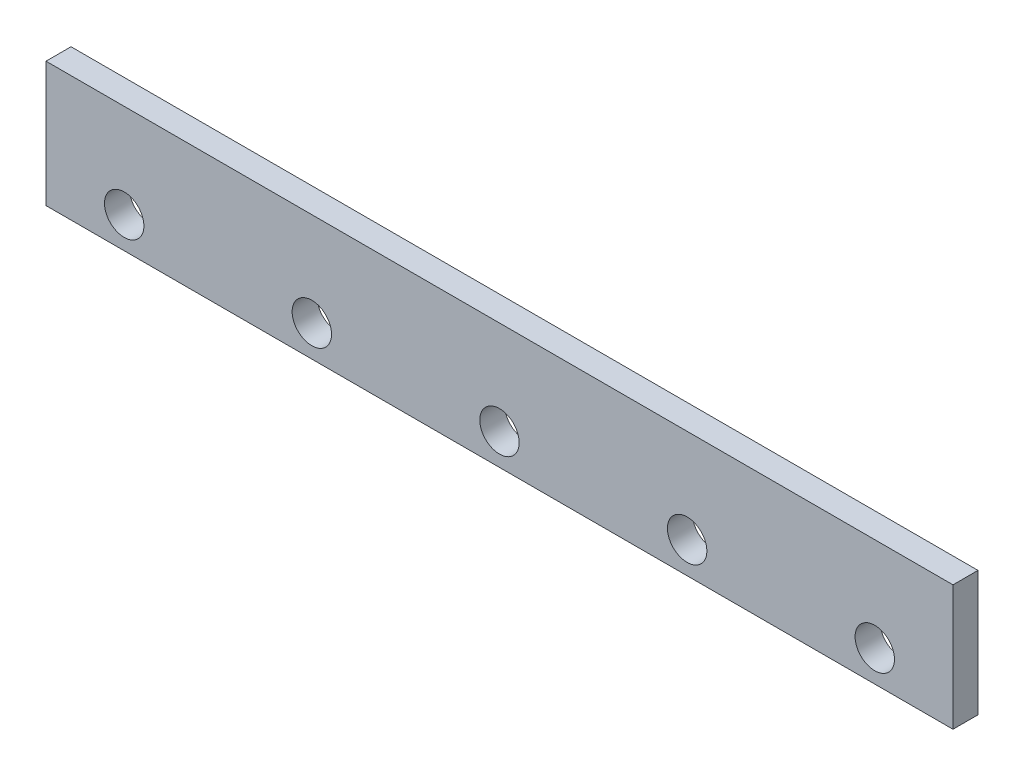
SolidWorks part; units mm, degrees
ref_plane "Front Plane" through (0, 0, 0) normal (0, 0, 1) x (1, 0, 0)
ref_plane "Top Plane" through (0, 0, 0) normal (0, 1, 0) x (1, 0, 0)
ref_plane "Right Plane" through (0, 0, 0) normal (1, 0, 0) x (0, 0, -1)
sketch "Sketch1" plane through (0, 0, 0) normal (0, 0, 1) x (1, 0, 0)
  line L1 (0, 0) -> (580, 0)
  line L2 (0, 0) -> (0, 80)
  line L3 (0, 80) -> (580, 80)
  line L4 (580, 0) -> (580, 80)
  dimension "D1" = 580
  dimension "D2" = 80
extrude "Boss-Extrude1" add sketch "Sketch1" along normal blind 16
sketch "Sketch2" plane through (0, 0, 16) normal (0, 0, 1) x (1, 0, 0)
  line L0 (0, 80) -> (0, 0) construction
  line L1 (0, 0) -> (580, 0) construction
  circle A0 centre (50, 20) radius 12.6
  circle A1 centre (170, 20) radius 12.6
  circle A2 centre (290, 20) radius 12.6
  circle A3 centre (410, 20) radius 12.6
  circle A4 centre (530, 20) radius 12.6
  dimension "D1" = 5
  dimension "D2" = 25.2
  dimension "D5" = 120
  dimension "D6" = 530
  dimension "D3" = 50
  dimension "D4" = 20
extrude "Cut-Extrude1" cut sketch "Sketch2" against normal blind 16
